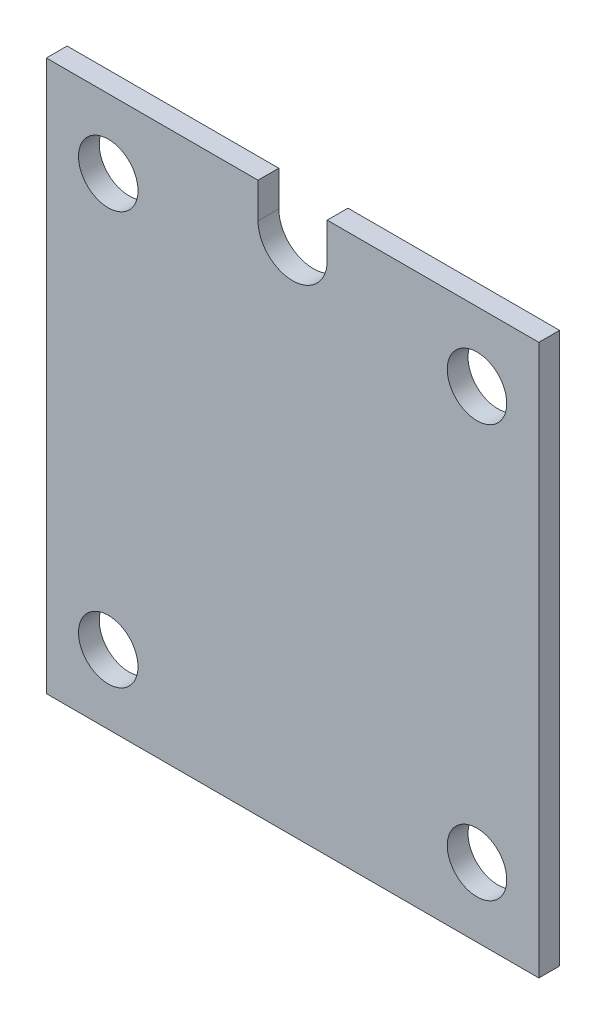
SolidWorks part; units mm, degrees
ref_plane "Front Plane" through (0, 0, 0) normal (0, 0, 1) x (1, 0, 0)
ref_plane "Top Plane" through (0, 0, 0) normal (0, 1, 0) x (1, 0, 0)
ref_plane "Right Plane" through (0, 0, 0) normal (1, 0, 0) x (0, 0, -1)
sketch "Sketch1" plane through (0, 0, 0) normal (0, 0, 1) x (1, 0, 0)
  line L0 (0, 34.7) -> (0, 58.7557) construction
  line L1 (-35.5928, -39.7849) -> (35.5928, -39.7849)
  line L2 (-35.5928, -39.7849) -> (-35.5928, 39.7849)
  line L3 (-35.5928, 39.7849) -> (35.5928, 39.7849)
  line L4 (35.5928, -39.7849) -> (35.5928, 39.7849)
  line L5 (-35.5928, -39.7849) -> (35.5928, 39.7849) construction
  line L6 (-35.5928, 39.7849) -> (35.5928, -39.7849) construction
  line L7 (-26.65, -29.8) -> (26.65, -29.8) construction
  line L8 (-26.65, -29.8) -> (-26.65, 29.8) construction
  line L9 (-26.65, 29.8) -> (26.65, 29.8) construction
  line L10 (26.65, -29.8) -> (26.65, 29.8) construction
  line L11 (-26.65, -29.8) -> (26.65, 29.8) construction
  line L12 (-26.65, 29.8) -> (26.65, -29.8) construction
  line L13 (-5, 34.7) -> (-5, 58.7557)
  line L14 (5, 34.7) -> (5, 58.7557)
  circle A0 centre (26.65, 29.8) radius 4.3
  circle A1 centre (26.65, -29.8) radius 4.3
  circle A2 centre (-26.65, -29.8) radius 4.3
  circle A3 centre (-26.65, 29.8) radius 4.3
  arc A5 (-5, 34.7) -> (5, 34.7) centre (0, 34.7) ccw
  arc A6 (5, 58.7557) -> (-5, 58.7557) centre (0, 58.7557) ccw
  point P0 (0, 0)
  point P6 (0, 0)
  point P15 (0, 46.7278)
  dimension "D1" = 8.6
  dimension "D4" = 4.9
  dimension "D5" = 10
  dimension "D2" = 59.6
  dimension "D3" = 53.3
extrude "Boss-Extrude1" add sketch "Sketch1" along normal blind 3 contours A5 L13 L3 L2 L1 L4 L14 A3 A2 A1 A0
